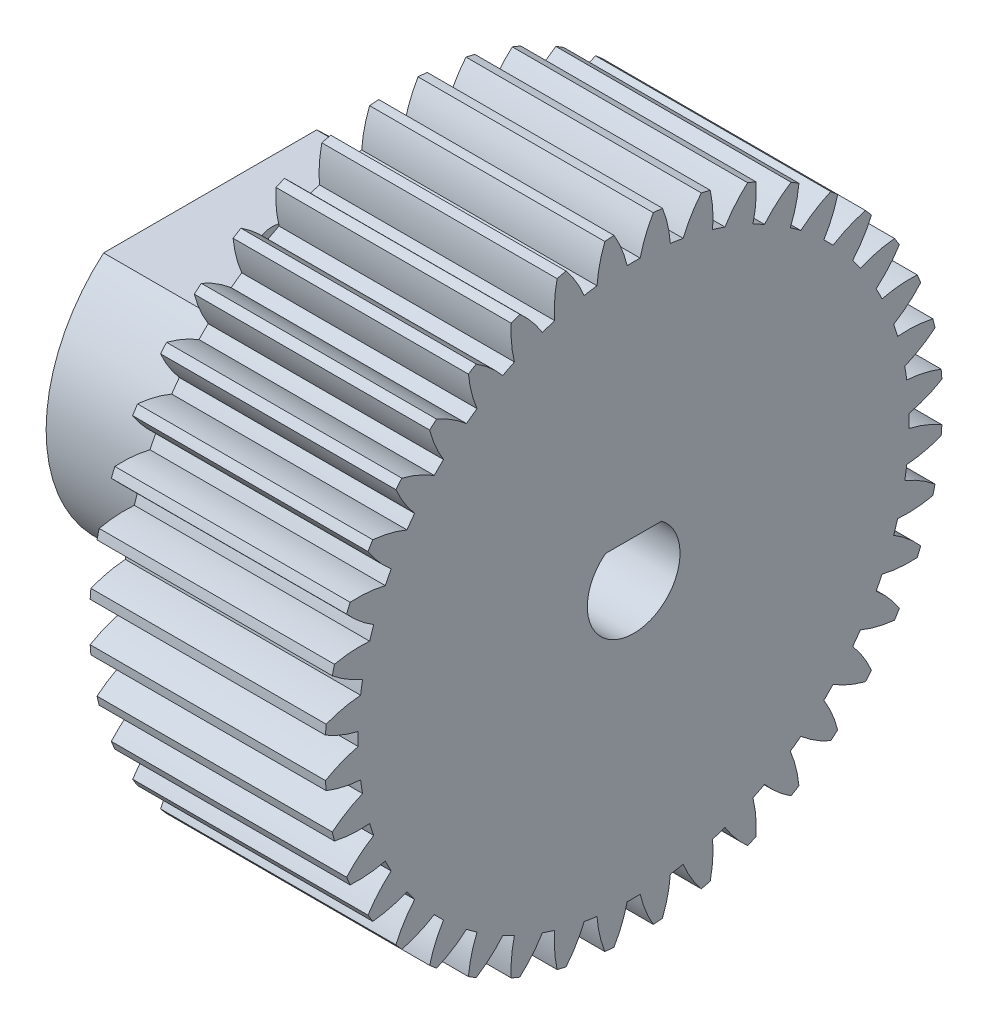
SolidWorks part; units mm, degrees
ref_plane "Plane1" through (0, 0, 0) normal (0, 0, 1) x (1, 0, 0)
ref_plane "Plane2" through (0, 0, 0) normal (0, 1, 0) x (1, 0, 0)
ref_plane "Plane3" through (0, 0, 0) normal (1, 0, 0) x (0, 0, -1)
sketch "HoldingSke" plane through (0, 0, 0) normal (0, 1, 0) x (1, 0, 0)
  line L0 (0, 0) -> (622.6409, -522.4578)
  line L1 (-15, 0) -> (100, 0) construction
  line L2 (0, 0) -> (-2.1039, 2.3779)
  line L3 (0, 0) -> (-11.863, 4.5341)
  line L4 (0, 0) -> (6.6156, 5.5511)
  line L5 (0, 0) -> (-47.5972, -17.7524)
  line L6 (0, 0) -> (-10.5278, -7.1032)
  line L7 (-2.1039, 2.3779) -> (8.8308, 51.9871)
  line L8 (-76.2, 54.61) -> (-71.1708, 54.61)
  line L9 (-71.009, 38.7566) -> (-53.1078, 45.2721)
  line L10 (-76.2, 71.12) -> (104.1128, 71.12)
  line L11 (0, 0) -> (-12.7, 0)
  line L12 (-76.2, 101.6) -> (-76.1716, 101.6)
  line L13 (24.9733, 27.94) -> (52.9518, 28.4284)
  line L14 (24.9733, 27.94) -> (25.0241, 27.9398)
  line L15 (24.9733, 27.94) -> (100.4021, 29.52)
  circle A0 centre (0, 0) radius 2.3812
  circle A1 centre (0, 0) radius 14.8717
  circle A2 centre (0, 0) radius 38.1
  circle A3 centre (0, 0) radius 2.3812
  dimension "MHD" = 29.7434
  dimension "Hub_dia" = 76.2
  dimension "Bore" = 4.7625
  dimension "MBD" = 4.7625
  dimension "Num_teeth" = 40
  dimension "Pitch" = 812.8
  dimension "Overall_len" = 50.8
  dimension "Show_teeth" = 40
  dimension "Thickness" = 12.7
  dimension "OAL" = 50.8001
  dimension "T_dim" = 5.0292
  dimension "Ap" = 20
  dimension "H" = 19.05
  dimension "Pitch_radius" = 180.3128
  dimension "Width" = 12.7
  dimension "Backlash" = 0.0284
  dimension "Addendum_fac" = 1
  dimension "Dedendum_fac" = 1.2
  dimension "Clearance_fac" = 0.2
  dimension "Dedendum_add" = 0.0508
sketch "BasProSke" plane through (0, 0, 0) normal (0, 1, 0) x (1, 0, 0)
  line L0 (-10, 0) -> (60, 0) construction
  line L1 (0, 0) -> (0, 16.6687)
  line L2 (0, 0) -> (12.7, 0)
  line L3 (12.7, 0) -> (12.7, 16.6687)
  line L4 (12.7, 16.6687) -> (0, 16.6687)
  dimension "Thickness" = 12.7
  dimension "Diameter" = 33.3375
revolve "Base-Revolve" add sketch "BasProSke" angle 360 about L0
sketch "TooCutSke" plane through (0, 0, 0) normal (1, 0, 0) x (0, 0, -1)
  line L1 (0, 0) -> (0, 107) construction
  line L2 (0, 0) -> (-0.673, 15.8607) construction
  line L3 (0, 0) -> (-2.4895, 31.6315) construction
  line L4 (-0.673, 15.8607) -> (-1.2447, 15.8157) construction
  arc A0 (0.3509, 14.8676) -> (-0.3509, 14.8676) centre (0, 0) ccw
  arc A1 (1.0752, 16.6595) -> (-1.0752, 16.6595) centre (0, 0) ccw
  circle A2 centre (0, 0) radius 15.875 construction
  circle A3 centre (0, 0) radius 14.9176 construction
  arc A4 (-0.3509, 14.8676) -> (-1.0752, 16.6595) centre (-6.5317, 13.4116) ccw
  arc A5 (1.0752, 16.6595) -> (0.3509, 14.8676) centre (6.5317, 13.4116) ccw
  dimension "Root_dia" = 29.7434
  dimension "Overcut_dia" = 33.3883
  dimension "Pitch_dia" = 31.75
  dimension "Base_dia" = 29.8352
  dimension "Flank_rad" = 6.35
  dimension "Half_ang" = 4.5
  dimension "Half_CT" = 0.5735
extrude "ToothCut" cut sketch "TooCutSke" along normal through all
fillet "Breaks" [suppressed] radius 0.0159
fillet "RootFillets" [suppressed] radius 0.2095
pattern_circular "TeethCuts" count 40 every 9 about axis through (-10, 0, 0) along (1, 0, 0) of "ToothCut", "RootFillets", "Breaks"
sketch "HubNeaOneSke" plane through (0, 0, 0) normal (-1, 0, 0) x (0, 0, 1)
  circle A0 centre (0, 0) radius 14.8717
  dimension "Diameter" = 29.7434
extrude "HubNearOne" [suppressed] add sketch "HubNeaOneSke" along normal blind 38.1001
sketch "HubNeaBotSke" plane through (0, 0, 0) normal (-1, 0, 0) x (0, 0, 1)
  circle A0 centre (0, 0) radius 14.8717
  dimension "Diameter" = 29.7434
extrude "HubNearBoth" [suppressed] add sketch "HubNeaBotSke" along normal blind 19.05
ref_plane "FarPln" through (12.7, 0, 0) normal (1, 0, 0) x (0, 0, -1)
sketch "HubFarSke" plane through (12.7, 0, 0) normal (1, 0, 0) x (0, 0, -1)
  circle A0 centre (0, 0) radius 14.8717
  dimension "Diameter" = 29.7434
extrude "HubFar" [suppressed] add sketch "HubFarSke" along normal blind 19.05
sketch "BorSke" plane through (0, 0, 0) normal (1, 0, 0) x (0, 0, -1)
  circle A0 centre (0, 0) radius 2.3812
  dimension "Diameter" = 4.7625
extrude "Bore" cut sketch "BorSke" along normal mid plane 101.6001
sketch "KeySke" plane through (0, 0, 0) normal (1, 0, 0) x (0, 0, -1)
  line L0 (-0.127, 0) -> (-0.127, 2.6479)
  line L1 (-0.127, 2.6479) -> (0.127, 2.6479)
  line L2 (0.127, 2.6479) -> (0.127, 0)
  line L3 (0, 0) -> (0, 34) construction
  line L4 (-0.127, 0) -> (0.127, 0)
  dimension "Offset" = 2.648
  dimension "Width" = 0.254
extrude "Keyway" [suppressed] cut sketch "KeySke" along normal mid plane 101.6001
pattern_circular "Keyway2" [suppressed] count 2 every 90 about axis through (-10, 0, 0) along (1, 0, 0)
sketch "Sketch1" plane through (12.7, 0, 0) normal (1, 0, 0) x (0, 0, -1)
  line L0 (0, 25.6558) -> (0, -26.1333) construction
  line L1 (-24.8431, 0) -> (25.1424, 0) construction
  line L2 (-20.32, 20.32) -> (-20.32, -20.32) construction
  line L3 (-20.32, -20.32) -> (20.32, -20.32) construction
  line L4 (20.32, -20.32) -> (20.32, 20.32) construction
  line L5 (20.32, 20.32) -> (-20.32, 20.32) construction
  circle A0 centre (-20.32, 20.32) radius 2.413
  circle A1 centre (20.32, 20.32) radius 2.413
  circle A2 centre (20.32, -20.32) radius 2.413
  circle A3 centre (-20.32, -20.32) radius 2.413
  point P7 (0, 20.32)
  point P10 (20.32, 0)
  dimension "D3" = 4.826
  dimension "D1" = 40.64
  dimension "D2" = 40.64
extrude "Cut-Extrude1" cut sketch "Sketch1" against normal up to surface (12.7 mm away)
sketch "Sketch2" plane through (12.7, 0, 0) normal (1, 0, 0) x (0, 0, -1)
  circle A0 centre (0, 0) radius 5.461
  dimension "D1" = 10.922
extrude "Cut-Extrude2" cut sketch "Sketch2" against normal up to surface (12.7 mm away) up to face at (0, 0, -2.3812)
sketch "Sketch3" plane through (12.7, 0, 0) normal (1, 0, 0) x (0, 0, -1)
  line L0 (-20.32, -20.32) -> (20.32, 20.32) construction
  line L1 (-20.32, 20.32) -> (20.32, -20.32) construction
  line L2 (19.794, -28.7742) -> (6.7711, -15.7513)
  line L3 (28.7742, -19.794) -> (15.7513, -6.7711)
  line L4 (-28.7742, -19.794) -> (-15.7513, -6.7711)
  line L5 (-19.794, -28.7742) -> (-6.7711, -15.7513)
  line L6 (-6.7711, 15.7513) -> (-19.794, 28.7742)
  line L7 (6.7711, 15.7513) -> (19.794, 28.7742)
  line L8 (-15.7513, 6.7711) -> (-28.7742, 19.794)
  line L12 (15.7513, 6.7711) -> (28.7742, 19.794)
  arc A0 (-28.7742, 19.794) -> (-28.7742, -19.794) centre (0, 0) ccw
  arc A1 (-15.7513, 6.7711) -> (-15.7513, -6.7711) centre (0, 0) ccw
  arc A2 (-6.7711, -15.7513) -> (6.7711, -15.7513) centre (0, 0) ccw
  arc A3 (15.7513, -6.7711) -> (15.7513, 6.7711) centre (0, 0) ccw
  arc A4 (6.7711, 15.7513) -> (-6.7711, 15.7513) centre (0, 0) ccw
  arc A5 (19.794, 28.7742) -> (-19.794, 28.7742) centre (0, 0) ccw
  arc A6 (28.7742, -19.794) -> (28.7742, 19.794) centre (0, 0) ccw
  arc A7 (-19.794, -28.7742) -> (19.794, -28.7742) centre (0, 0) ccw
  dimension "D1" = 69.85
  dimension "D2" = 17.78
  dimension "D3" = 12.7
  dimension "D4" = 12.7
extrude "Cut-Extrude3" cut sketch "Sketch3" against normal up to surface (12.7 mm away)
sketch "Sketch4" plane through (12.7, 0, 0) normal (1, 0, 0) x (0, 0, -1)
  circle A0 centre (0, 0) radius 2.5019
  circle A1 centre (0, 0) radius 5.461
  circle A2 centre (0, 0) radius 5.461 construction
  dimension "D1" = 5.0038
extrude "Boss-Extrude1" add sketch "Sketch4" against normal up to surface (12.7 mm away) up to face at (0, 0, -5.461)
sketch "Sketch5" plane through (12.7, 0, 0) normal (1, 0, 0) x (0, 0, -1)
  line L0 (-1.5112, 1.9939) -> (1.5112, 1.9939)
  line L1 (-1.6042, -2.5019) -> (1.6042, -2.5019) construction
  circle A0 centre (0, 0) radius 2.5019 construction
  arc A1 (-1.5112, 1.9939) -> (1.5112, 1.9939) centre (0, 0) cw
  point P6 (0, -2.5019)
  point P7 (0, 1.9939)
  dimension "D1" = 4.4958
extrude "Boss-Extrude2" add sketch "Sketch5" against normal up to surface (12.7 mm away) up to face at (0, 0, 0)
sketch "Sketch6" plane through (0, 0, 0) normal (-1, 0, 0) x (0, 0, 1)
  line L0 (-5.7489, 6.731) -> (5.7489, 6.731)
  line L1 (-1.5112, 1.9939) -> (1.5112, 1.9939) construction
  circle A0 centre (0, 0) radius 2.5019
  arc A1 (-1.5112, 1.9939) -> (1.5112, 1.9939) centre (0, 0) ccw construction
  arc A2 (-5.7489, 6.731) -> (5.7489, 6.731) centre (0, 0) ccw
  point P11 (0, 1.9939)
  point P12 (0, 6.731)
  dimension "D1" = 6.35
  dimension "D2" = 6.731
extrude "Boss-Extrude3" add sketch "Sketch6" along normal blind 10.16
sketch "Sketch8" plane through (0, 6.731, 0) normal (0, 1, 0) x (1, 0, 0)
  line L0 (0, -5.7489) -> (0, 5.7489) construction
  circle A0 centre (-5.08, 0) radius 1.7526
  dimension "D1" = 3.5052
  dimension "D2" = 5.08
extrude "Cut-Extrude4" cut sketch "Sketch8" against normal up to surface (4.9455 mm away)
equation "' \"Pitch@HoldingSke\" = 4"
equation "' \"Num_teeth@HoldingSke\" = 12"
equation "' \"Ap@HoldingSke\" =  20"
equation "' \"Ap@HoldingSke\" = 20"
equation "' \"Width@HoldingSke\" = 0.5"
equation "' \"Hub_dia@HoldingSke\"= 1"
equation "' \"Hub_dia@HoldingSke\" = 1"
equation "' \"Overall_len@HoldingSke\" = 1.0"
equation "' \"Bore@HoldingSke\" = 0.75"
equation "' \"T_dim@HoldingSke\" = 0.85"
equation "' \"Width@KeySke\" = 0.25"
equation "' \"Show_teeth@HoldingSke\" = 13"
equation "' \"Backlash@HoldingSke\" = 0.009"
equation "' \"Addendum_fac@HoldingSke\" = 1.0"
equation "' \"Dedendum_fac@HoldingSke\" = 1.25"
equation "' \"Dedendum_add@HoldingSke\" = 0.00005"
equation "' \"Clearance_fac@HoldingSke\" = 0.25"
equation "' \"Pitch@HoldingSke\" = 0.5"
equation "' \"Num_teeth@HoldingSke\" = 23"
equation "' \"Show_teeth@HoldingSke\" = 23"
equation "' \"Backlash@HoldingSke\" = 0.0375"
equation "\"Overcut_dia@TooCutSke\" = (\"Num_teeth@HoldingSke\" + 2 * \"Addendum_fac@HoldingSke\") / \"Pitch@HoldingSke\" + 0.002"
equation "\"Pitch_dia@TooCutSke\" = \"Num_teeth@HoldingSke\" / \"Pitch@HoldingSke\""
equation "\"Base_dia@TooCutSke\" = \"Num_teeth@HoldingSke\" / \"Pitch@HoldingSke\" * cos((\"Ap@HoldingSke\"  * 3.14159265 / 180))"
equation "\"Root_dia@TooCutSke\" = (\"Num_teeth@HoldingSke\" + 2) / \"Pitch@HoldingSke\" - 2 * (\"Addendum_fac@HoldingSke\" + \"Dedendum_fac@HoldingSke\") / \"Pitch@HoldingSke\" - \"Dedendum_add@HoldingSke\" * 2"
equation "\"Half_ang@TooCutSke\" = 180 / \"Num_teeth@HoldingSke\""
equation "\"Half_CT@TooCutSke\" = \"Num_teeth@HoldingSke\" / \"Pitch@HoldingSke\" * sin((3.14159265 / 2 / \"Num_teeth@HoldingSke\")) / 2 - 7 * \"Backlash@HoldingSke\" / 4"
equation "\"Flank_rad@TooCutSke\" = \"Num_teeth@HoldingSke\" / \"Pitch@HoldingSke\" / 5"
equation "\"Radius@RootFillets\" = \"Clearance_fac@HoldingSke\" / \"Pitch@HoldingSke\" + \"Dedendum_add@HoldingSke\""
equation "\"Break_rad@Breaks\" = 0.02 / \"Pitch@HoldingSke\""
equation "\"Thickness@HoldingSke\" = \"Width@HoldingSke\""
equation "\"OAL@HoldingSke\" = \"Thickness@HoldingSke\""
equation "\"MHD@HoldingSke\" = (\"Num_teeth@HoldingSke\" + 2) / \"Pitch@HoldingSke\" - 2 * (\"Addendum_fac@HoldingSke\" + \"Dedendum_fac@HoldingSke\")  / \"Pitch@HoldingSke\" - \"Dedendum_add@HoldingSke\" * 2"
equation "\"MBD@HoldingSke\" = (\"Num_teeth@HoldingSke\" + 2) / \"Pitch@HoldingSke\" - 2 * (\"Addendum_fac@HoldingSke\" + \"Dedendum_fac@HoldingSke\")  / \"Pitch@HoldingSke\" - \"Dedendum_add@HoldingSke\" * 2 - 0.002"
equation "\"MHD@HoldingSke\" = ((sgn( \"MHD@HoldingSke\" - \"Hub_dia@HoldingSke\" )-1)*( \"MHD@HoldingSke\" - \"Hub_dia@HoldingSke\" ))/-2+ \"Hub_dia@HoldingSke\""
equation "\"MBD@HoldingSke\" = ((sgn( \"MBD@HoldingSke\" - \"Bore@HoldingSke\" )-1)*( \"MBD@HoldingSke\" - \"Bore@HoldingSke\" ))/-2+ \"Bore@HoldingSke\""
equation "\"OAL@HoldingSke\" = ((sgn( \"OAL@HoldingSke\" - \"Overall_len@HoldingSke\" )+1)*( \"OAL@HoldingSke\" - \"Overall_len@HoldingSke\" ))/2 + \"Overall_len@HoldingSke\" + 0.000002"
equation "\"Num_teeth@TeethCuts\" = int( \"Show_teeth@HoldingSke\" ) + 1"
equation "\"Num_teeth@TeethCuts\" = ((sgn( \"Num_teeth@TeethCuts\" - \"Num_teeth@HoldingSke\" )-1)*( \"Num_teeth@TeethCuts\" - \"Num_teeth@HoldingSke\" ))/-2+ \"Num_teeth@HoldingSke\""
equation "\"Num_teeth@TeethCuts\" = ((sgn( \"Num_teeth@TeethCuts\" - 2.0)+1)*( \"Num_teeth@TeethCuts\" - 2.0))/2 +2.0"
equation "\"Angle@TeethCuts\" = 360.0 / \"Num_teeth@HoldingSke\""
equation "\"Diameter@BasProSke\" = (\"Num_teeth@HoldingSke\" + 2 * \"Addendum_fac@HoldingSke\") / \"Pitch@HoldingSke\""
equation "\"Thickness@BasProSke\"  = \"Thickness@HoldingSke\""
equation "' \"Fillet_rad@BasProSke\" =  \"Thickness@HoldingSke\" * 0.05"
equation "' \"Fillet_rad@BasProSke\" = \"Thickness@HoldingSke\" * 0.05"
equation "\"MHD@HoldingSke\" = ((sgn( \"MHD@HoldingSke\" - \"Root_dia@TooCutSke\" )-1)*( \"MHD@HoldingSke\" - \"Root_dia@TooCutSke\" ))/-2+ \"Root_dia@TooCutSke\""
equation "\"Diameter@HubNeaOneSke\" = \"MHD@HoldingSke\""
equation "\"Length@HubNearOne\" = \"OAL@HoldingSke\" - \"Thickness@BasProSke\""
equation "\"Diameter@HubNeaBotSke\" = \"MHD@HoldingSke\""
equation "\"Length@HubNearBoth\" = ( \"OAL@HoldingSke\" - \"Thickness@BasProSke\" ) / 2.0"
equation "\"Thickness@FarPln\" = \"Thickness@BasProSke\""
equation "\"Diameter@HubFarSke\" = \"MHD@HoldingSke\""
equation "\"Length@HubFar\" = ( \"OAL@HoldingSke\" - \"Thickness@BasProSke\" ) / 2.0"
equation "\"Diameter@BorSke\" = \"MBD@HoldingSke\""
equation "\"D1@Bore\" = \"OAL@HoldingSke\" * 2.0"
equation "\"D1@Keyway\" = \"OAL@HoldingSke\" * 2.0"
equation "\"Offset@KeySke\" = \"T_dim@HoldingSke\" - \"MBD@HoldingSke\" / 2.0"
equation "\"o.5\"=0.672596"
